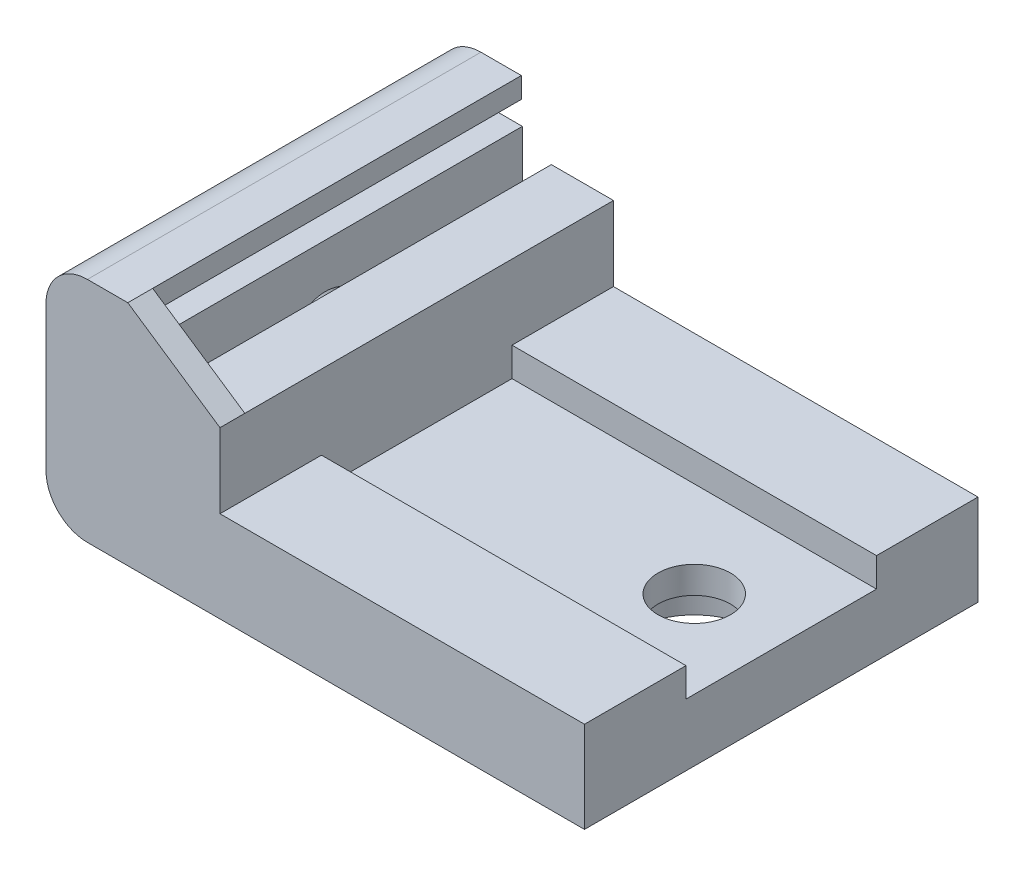
SolidWorks part; units mm, degrees
ref_plane "Front Plane" through (0, 0, 0) normal (0, 0, 1) x (1, 0, 0)
ref_plane "Top Plane" through (0, 0, 0) normal (0, 1, 0) x (1, 0, 0)
ref_plane "Right Plane" through (0, 0, 0) normal (1, 0, 0) x (0, 0, -1)
sketch "Sketch2" plane through (0, 0, 0) normal (0, 1, 0) x (1, 0, 0)
  line L1 (0, 0) -> (23, 0)
  line L2 (0, 0) -> (0, 19)
  line L3 (0, 19) -> (23, 19)
  line L4 (23, 0) -> (23, 19)
  line L5 (0, 0) -> (23, 19) construction
  line L6 (0, 19) -> (23, 0) construction
  point P4 (11.5, 9.5)
  dimension "D1" = 19
  dimension "D2" = 23
extrude "Boss-Extrude1" add sketch "Sketch2" along normal blind 3
sketch "Sketch3" plane through (0, 3, 0) normal (0, 1, 0) x (1, 0, 0)
  line L0 (0, 0) -> (23, 0) construction
  line L1 (0, 19) -> (1, 19)
  line L2 (0, 19) -> (0, 0)
  line L3 (0, 0) -> (1, 0)
  line L4 (1, 19) -> (1, 0)
  line L5 (0, 19) -> (1, 0) construction
  line L6 (0, 0) -> (1, 19) construction
  line L7 (23, 19) -> (0, 19) construction
  line L8 (2.4, 0) -> (5.4, 0)
  line L9 (2.4, 0) -> (2.4, 19)
  line L10 (2.4, 19) -> (5.4, 19)
  line L11 (5.4, 0) -> (5.4, 19)
  line L12 (2.4, 0) -> (5.4, 19) construction
  line L13 (2.4, 19) -> (5.4, 0) construction
  point P4 (0.5, 9.5)
  point P12 (3.9, 9.5)
  line M9 (0, 19) -> (0, 0)
  line M10 (0, 0) -> (23, 0)
  line M12 (23, 19) -> (0, 19)
  dimension "D1" = 1
  dimension "D2" = 3
  dimension "D3" = 1.4
extrude "Boss-Extrude2" add sketch "Sketch3" along normal blind 5 contours L4 M12 M9 M10 | L11 L9 M10 M12
sketch "Sketch4" plane through (0, 0, -19) normal (0, 0, -1) x (-1, 0, 0)
  line L0 (-1, 8) -> (0, 8) construction
  line L1 (0, 0) -> (3, 0)
  line L2 (0, 0) -> (0, 8)
  line L3 (0, 8) -> (1.5, 8)
  line L4 (3, 0) -> (3, 8)
  line L5 (0, 0) -> (3, 8) construction
  line L6 (0, 8) -> (3, 0) construction
  line L7 (3, 8) -> (3, 11)
  line L8 (3, 11) -> (-0.95, 11)
  line L9 (-0.95, 11) -> (-0.95, 10)
  line L10 (-0.95, 10) -> (1.5, 10)
  line L11 (1.5, 10) -> (1.5, 8)
  line L12 (1.5, 8) -> (3, 8) construction
  line L14 (-1, 8) -> (-1, 3) construction
  point P4 (1.5, 4)
  dimension "D1" = 0.05
  dimension "D2" = 2
  dimension "D3" = 3
  dimension "D4" = 1
  dimension "D5" = 1.5
extrude "Boss-Extrude3" add sketch "Sketch4" against normal up to surface (19 mm away) up to face at (6.36, 4.4, 0)
sketch "Sketch5" plane through (0, 3, 0) normal (0, 1, 0) x (1, 0, 0)
  line L0 (23, 9.5) -> (7.632, 9.5) construction
  line L1 (23, 0) -> (23, 19) construction
  line L2 (5.4, 0) -> (5.4, 19) construction
  circle A0 centre (18.8, 9.5) radius 1.75
  dimension "D1" = 13.4
  dimension "D2" = 3.5
extrude "Cut-Extrude1" cut sketch "Sketch5" against normal through all
sketch "Sketch6" plane through (0, 0, 0) normal (0, -1, 0) x (1, 0, 0)
  circle A0 centre (18.8, -9.5) radius 3
  dimension "D1" = 6
extrude "Cut-Extrude2" cut sketch "Sketch6" against normal blind 1.7
sketch "Sketch7" plane through (0, 3, 0) normal (0, 1, 0) x (1, 0, 0)
  line L0 (5.4, 0) -> (5.4, 19) construction
  line L1 (5.4, 0) -> (23, 0)
  line L2 (5.4, 0) -> (5.4, 4.9)
  line L3 (5.4, 4.9) -> (23, 4.9)
  line L4 (23, 0) -> (23, 4.9)
  line L5 (5.4, 0) -> (23, 4.9) construction
  line L6 (5.4, 4.9) -> (23, 0) construction
  line L7 (23, 0) -> (23, 19) construction
  line L9 (23, 14.1) -> (5.4, 14.1)
  line L10 (23, 14.1) -> (23, 19)
  line L11 (23, 19) -> (5.4, 19)
  line L12 (5.4, 14.1) -> (5.4, 19)
  line L13 (23, 14.1) -> (5.4, 19) construction
  line L14 (23, 19) -> (5.4, 14.1) construction
  line L16 (5.4, 0) -> (23, 0) construction
  point P4 (14.2, 2.45)
  point P13 (14.2, 16.55)
  dimension "D3" = 9.2
extrude "Boss-Extrude4" add sketch "Sketch7" along normal blind 1.4
sketch "Sketch8" plane through (0, 0, -19) normal (0, 0, -1) x (-1, 0, 0)
  line L0 (1.5, 10) -> (1.5, 8) construction
  line L1 (-1, 8) -> (1.5, 8)
  line L2 (-1, 8) -> (-1, 8.9)
  line L3 (-1, 8.9) -> (1.5, 8.9)
  line L4 (1.5, 8) -> (1.5, 8.9)
  line L5 (-1, 8) -> (1.5, 8.9) construction
  line L6 (-1, 8.9) -> (1.5, 8) construction
  point P4 (0.25, 8.45)
  dimension "D1" = 0.9
extrude "Boss-Extrude5" add sketch "Sketch8" against normal up to surface (19 mm away) up to face at (4.0357, 6.3429, 0)
sketch "Sketch9" plane through (0, 0, -19) normal (0, 0, -1) x (-1, 0, 0)
  line L0 (-1, 3) -> (-1, 2.2)
  line L1 (-1, 2.2) -> (-2.4, 2.2)
  line L2 (-2.4, 2.2) -> (-2.4, 3)
  line L3 (-2.4, 3) -> (-1, 3)
  dimension "D1" = 0.8
extrude "Cut-Extrude3" cut sketch "Sketch9" against normal through all
sketch "Sketch10" plane through (0, 0, 0) normal (0, 0, 1) x (1, 0, 0)
  line L0 (-1.5, 8.9) -> (-1.5, 10)
  line L1 (-1.5, 10) -> (0.95, 10)
  line L2 (0.95, 10) -> (0.95, 11)
  line L3 (0.95, 11) -> (5.4, 8)
  line L4 (5.4, 8) -> (2.4, 8)
  line L5 (2.4, 8) -> (2.4, 2.2)
  line L6 (2.4, 2.2) -> (1, 2.2)
  line L7 (1, 2.2) -> (1, 8.9)
  line L8 (1, 8.9) -> (-1.5, 8.9)
extrude "Boss-Extrude6" add sketch "Sketch10" against normal blind 1.2
sketch "Sketch11" plane through (-3, 0, 0) normal (-1, 0, 0) x (0, 0, 1)
  line L0 (0, 5) -> (-19, 5) construction
  line L1 (0, 11) -> (0, 0) construction
  line L2 (-19, 0) -> (-19, 11) construction
  line L3 (0, 0) -> (-19, 0) construction
  circle A0 centre (-9.5, 5) radius 1.75
  dimension "D1" = 3.5
  dimension "D2" = 5
extrude "Cut-Extrude4" cut sketch "Sketch11" against normal up to next
fillet "Fillet1" radius 2 1 edges at (-3, 11, -9.5)
fillet "Fillet2" radius 2 1 edges at (-3, 0, -9.5)
